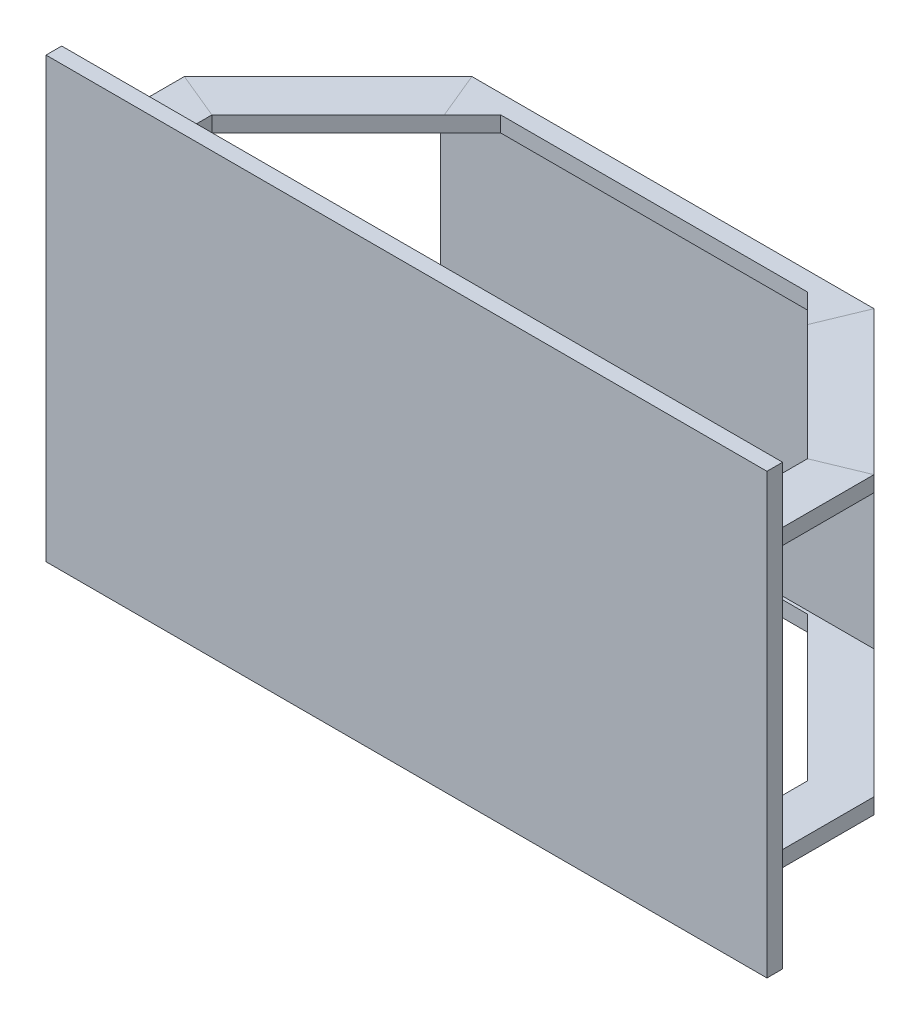
SolidWorks part; units mm, degrees
ref_plane "Plan de face" through (0, 0, 0) normal (0, 0, 1) x (1, 0, 0)
ref_plane "Plan de dessus" through (0, 0, 0) normal (0, 1, 0) x (1, 0, 0)
ref_plane "Plan de droite" through (0, 0, 0) normal (1, 0, 0) x (0, 0, -1)
sketch "Sketch1" plane through (0, 0, 0) normal (0, 0, 1) x (1, 0, 0)
  line L0 (0, 70) -> (0, -70) construction
  line L1 (-115, 70) -> (115, 70)
  line L2 (-115, 70) -> (-115, -70)
  line L3 (-115, -70) -> (115, -70)
  line L4 (115, 70) -> (115, -70)
  point P7 (0, 0)
  dimension "D1" = 230
  dimension "D2" = 140
extrude "Boss-Extrude1" add sketch "Sketch1" along normal blind 5
sketch "Sketch3" plane through (0, 0, 5) normal (0, 0, 1) x (1, 0, 0)
  line L0 (0, 70) -> (0, -70) construction
  line L1 (115, 70) -> (-115, 70) construction
  line L2 (-115, -70) -> (115, -70) construction
  line L3 (-115, 70) -> (-115, -70) construction
  line L4 (-110, 47) -> (-95, 47)
  line L5 (-110, 47) -> (-110, -47)
  line L6 (-110, -47) -> (-95, -47)
  line L7 (-95, 47) -> (-95, -47)
  line L8 (-115, 0) -> (115, 0) construction
  line L9 (115, -70) -> (115, 70) construction
  line L10 (95, 47) -> (95, -47)
  line L11 (110, -47) -> (95, -47)
  line L12 (110, 47) -> (110, -47)
  line L13 (110, 47) -> (95, 47)
  line L14 (22, 58) -> (22, 70)
  line L15 (-22, -58) -> (22, -58)
  line L16 (-22, -58) -> (-22, -70)
  line L17 (-22, -70) -> (22, -70)
  line L18 (22, -58) -> (22, -70)
  line L19 (-22, 70) -> (22, 70)
  line L20 (-22, 58) -> (-22, 70)
  line L21 (-22, 58) -> (22, 58)
  dimension "D1" = 15
  dimension "D2" = 5
  dimension "D3" = 94
  dimension "D4" = 44
  dimension "D5" = 12
sketch "Sketch4" plane through (0, 0, 0) normal (0, 0, 1) x (1, 0, 0)
  line L0 (0, 70) -> (0, -70) construction
  line L4 (-110, 47) -> (-95, 47)
  line L5 (-110, 47) -> (-110, -47)
  line L6 (-110, -47) -> (-95, -47)
  line L7 (-95, 47) -> (-95, -47)
  line L8 (-115, 0) -> (115, 0) construction
  dimension "D1" = 15
  dimension "D3" = 94
sketch "Sketch5" plane through (0, 0, 0) normal (0, 1, 0) x (1, 0, 0)
  line L0 (-100, 0) -> (-100, 30)
  line L1 (-115, 0) -> (115, 0) construction
  line L2 (-100, 30) -> (-60, 70)
  line L3 (-60, 70) -> (60, 70)
  line L4 (60, 70) -> (100, 30)
  line L5 (100, 30) -> (100, 0)
  line L6 (0, 70) -> (0, 0) construction
  dimension "D1" = 70
  dimension "D2" = 30
  dimension "D3" = 15
  dimension "D4" = 40
sweep "Sweep3" add profiles "Sketch4" path "Sketch5"
sketch "Sketch6" plane through (0, 47, 0) normal (0, 1, 0) x (1, 0, 0)
  line L2 (-48.9289, 74) -> (48.9289, 74)
  line L3 (-64.1421, 80) -> (64.1421, 80) construction
  line L4 (-48.9289, 74) -> (-76.4645, 46.4645)
  line L5 (-95, 27.9289) -> (-57.9289, 65) construction
  line L6 (48.9289, 74) -> (76.4645, 46.4645)
  line L7 (57.9289, 65) -> (95, 27.9289) construction
  line L8 (-76.4645, 46.4645) -> (76.4645, 46.4645)
  dimension "D1" = 6
extrude "Cut-Extrude1" cut sketch "Sketch6" against normal through all
sketch "Sketch7" plane through (-110, 0, 0) normal (-1, 0, 0) x (0, 0, 1)
  line L0 (-80, -47) -> (-80, 47) construction
  line L1 (-3, 42) -> (-75, 42)
  line L2 (-3, 42) -> (-3, -42)
  line L3 (-3, -42) -> (-75, -42)
  line L4 (-75, 42) -> (-75, -42)
  line L5 (0, 70) -> (0, -70) construction
  line L7 (0, 0) -> (-34.1421, 0) construction
  line L8 (0, 47) -> (0, -47) construction
  line L9 (-34.1421, -47) -> (-34.1421, 47) construction
  line L10 (0, -47) -> (-34.1421, -47) construction
  dimension "D1" = 5
  dimension "D2" = 3
  dimension "D3" = 5
extrude "Cut-Extrude2" cut sketch "Sketch7" against normal through all
sketch "Sketch8" plane through (0, 0, -80) normal (0, 0, -1) x (-1, 0, 0)
  line L1 (38.423, -43.0194) -> (-41.577, -43.0194)
  line L2 (38.423, -43.0194) -> (38.423, 36.9806)
  line L3 (38.423, 36.9806) -> (-41.577, 36.9806)
  line L4 (-41.577, -43.0194) -> (-41.577, 36.9806)
  dimension "D1" = 80
